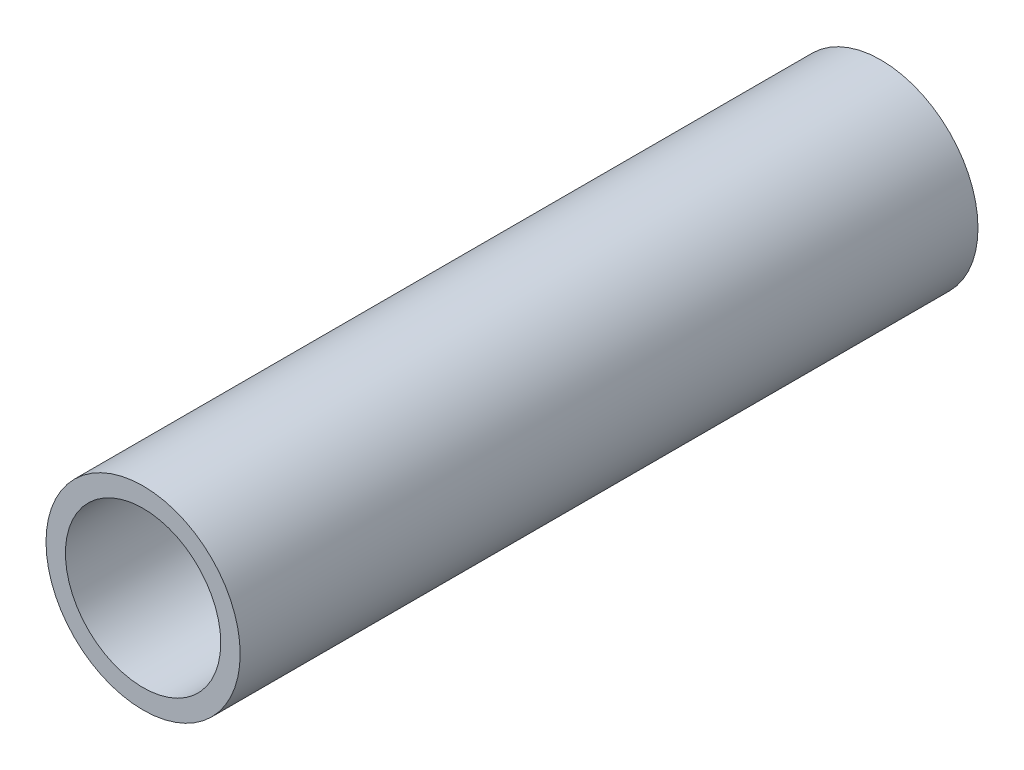
SolidWorks part; units mm, degrees
ref_plane "Front Plane" through (0, 0, 0) normal (0, 0, 1) x (1, 0, 0)
ref_plane "Top Plane" through (0, 0, 0) normal (0, 1, 0) x (1, 0, 0)
ref_plane "Right Plane" through (0, 0, 0) normal (1, 0, 0) x (0, 0, -1)
sketch "Sketch1" plane through (0, 0, 0) normal (0, 0, 1) x (1, 0, 0)
  circle A0 centre (0, 0) radius 1.25
  circle A1 centre (0, 0) radius 1
extrude "Boss-Extrude1" add sketch "Sketch1" along normal blind 9.5
equation "\"D1@Boss-Extrude1\"= 9.5 'Tube DIP Length"
